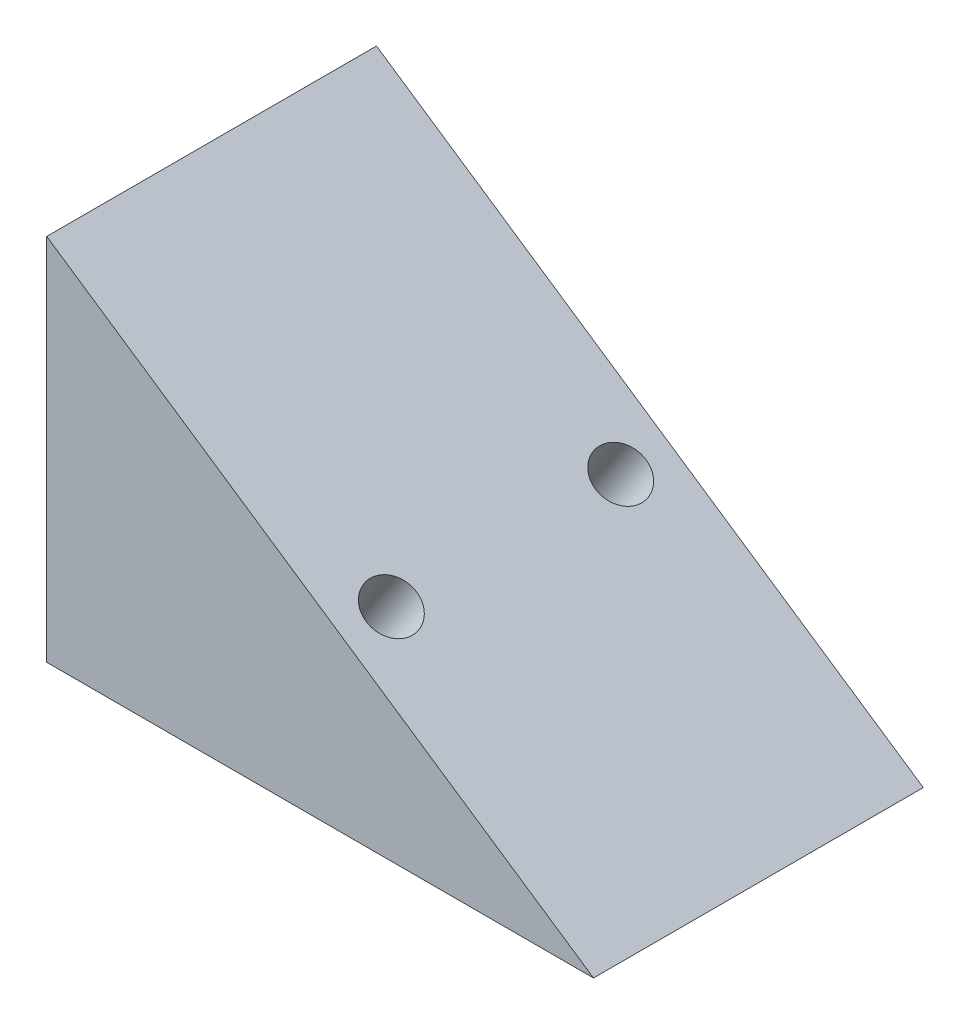
SolidWorks part; units mm, degrees
ref_plane "Plan de face" through (0, 0, 0) normal (0, 0, 1) x (1, 0, 0)
ref_plane "Plan de dessus" through (0, 0, 0) normal (0, 1, 0) x (1, 0, 0)
ref_plane "Plan de droite" through (0, 0, 0) normal (1, 0, 0) x (0, 0, -1)
sketch "Esquisse2" plane through (0, 0, 0) normal (0, 0, 1) x (1, 0, 0)
  line L0 (0, 0) -> (-215.5498, 0)
  line L1 (-215.5498, 0) -> (-215.5498, 145.3902)
  line L2 (-215.5498, 145.3902) -> (0, 0)
  dimension "D1" = 56
  dimension "D2" = 260
  dimension "D3" = 90
  dimension "D4" = 34
  dimension "D5" = 145.3902
  dimension "D6" = 215.5498
extrude "Boss.-Extru.1" add sketch "Esquisse2" along normal blind 130
sketch "Esquisse3" plane through (0, 0, 0) normal (0.5592, 0.829, 0) x (0.829, -0.5592, 0)
  line L0 (-1000, 0) -> (49000, 0) construction
  line L1 (-130, -1000) -> (-130, 49000) construction
  line L2 (0, 0) -> (-260, 0) construction
  line L3 (-1120, -65) -> (48880, -65) construction
  line L4 (0, -130) -> (0, 0) construction
  line L5 (-120, -1000) -> (-120, 49000) construction
  line L6 (-1110, -20) -> (48890, -20) construction
  circle A0 centre (-120, -19.8028) radius 10
  circle A1 centre (-120, -110.1972) radius 10
  point P8 (-130, 0)
  dimension "D1" = 65
  dimension "D2" = 130
  dimension "D3" = 10
  dimension "D4" = 20
extrude "Enlèv. mat.-Extru.1" cut sketch "Esquisse3" against normal blind 40
fillet "Congé1" radius 2 1 edges at (-130.1426, 39.5336, 19.8028)
fillet "Congé2" radius 2 1 edges at (-113.5618, 28.3497, 110.1972)
